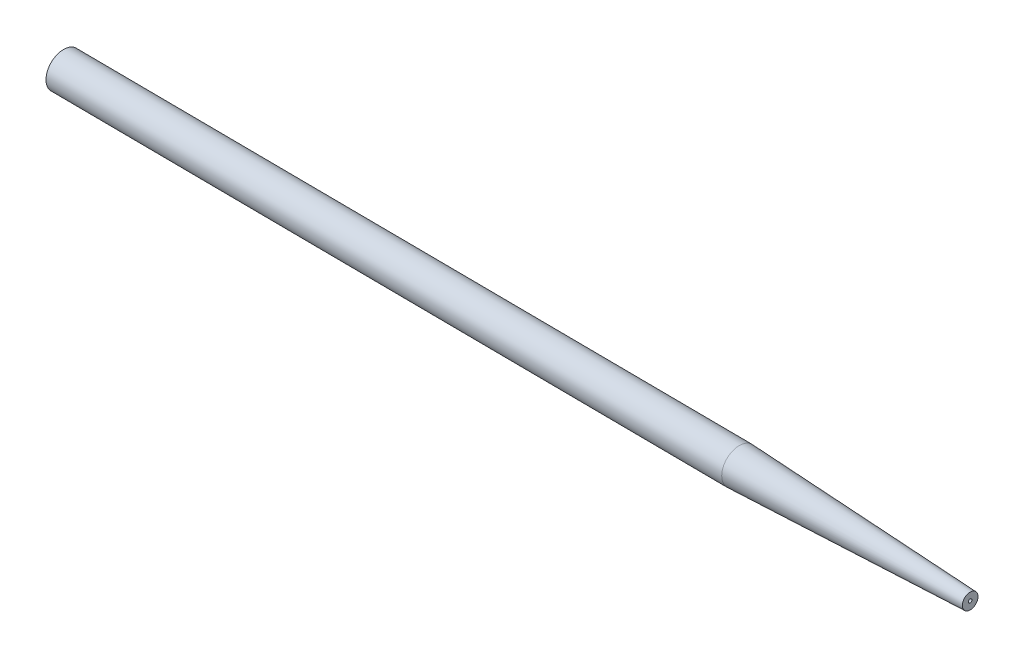
SolidWorks part; units mm, degrees
ref_plane "Front Plane" through (0, 0, 0) normal (0, 0, 1) x (1, 0, 0)
ref_plane "Top Plane" through (0, 0, 0) normal (0, 1, 0) x (1, 0, 0)
ref_plane "Right Plane" through (0, 0, 0) normal (1, 0, 0) x (0, 0, -1)
sketch "linear trace" plane through (0, 0, 0) normal (0, 1, 0) x (1, 0, 0)
  line L0 (544, 1224) -> (2720, 1224) construction
  line L1 (11.5196, 76.6077) -> (108.3137, 75.8702)
  line L2 (108.3137, 79.0702) -> (108.3137, 71.0411) construction
  line L3 (108.3137, 75.8702) -> (141.3808, 75.3617)
  line L4 (11.5196, 79.0702) -> (11.5196, 73.4998) construction
  line L5 (141.3808, 75.3617) -> (174.3828, 74.938)
  line L6 (177.6828, 75.893) -> (179.2802, 76.931)
  line L7 (174.3828, 76.931) -> (174.3828, 71.0411) construction
  arc A0 (174.3828, 74.938) -> (177.6828, 75.893) centre (174.4587, 80.8547) ccw
sketch "Sketch2" plane through (0, 0, 0) normal (0, 1, 0) x (1, 0, 0)
  line L0 (11.5196, 76.6077) -> (108.3137, 75.8702) construction
  line L1 (108.3137, 75.8702) -> (141.3808, 75.3617) construction
  line L3 (11.5196, 76.6077) -> (108.3137, 75.8702)
  line L4 (108.3137, 75.8702) -> (141.3808, 75.3617)
  line L6 (11.5196, 76.6077) -> (11.5196, 74.1077)
  line L7 (11.5196, 74.1077) -> (108.3137, 73.3702)
  line L8 (141.3808, 75.3617) -> (141.3808, 74.515)
  arc A0 (108.3137, 73.3702) -> (141.3808, 74.515) centre (137.7025, -297.367) cw
  dimension "D1" = 2.5
revolve "Revolve1" add sketch "Sketch2" angle 360 about L3
